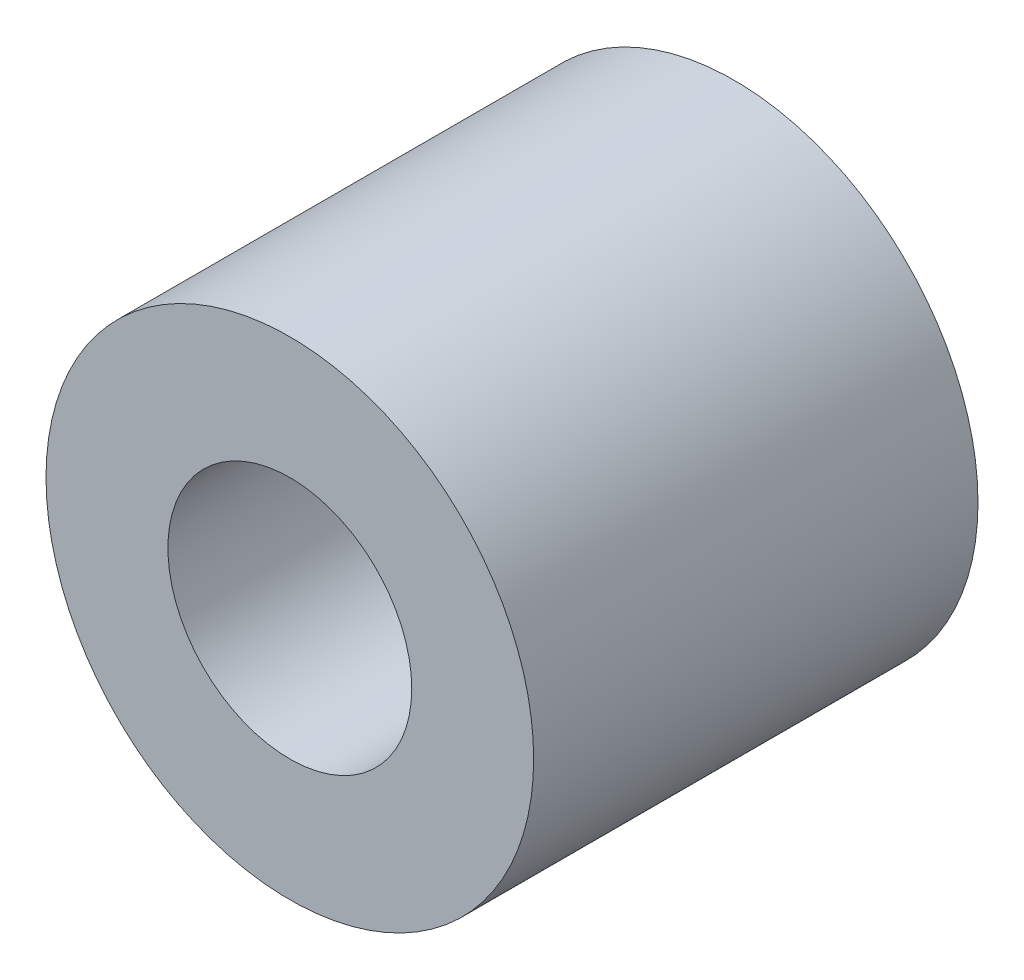
SolidWorks part; units mm, degrees
material "瞎编数据的PLA"
ref_plane "前视基准面" through (0, 0, 0) normal (0, 0, 1) x (1, 0, 0)
ref_plane "上视基准面" through (0, 0, 0) normal (0, 1, 0) x (1, 0, 0)
ref_plane "右视基准面" through (0, 0, 0) normal (1, 0, 0) x (0, 0, -1)
sketch "草图1" plane through (0, 0, 0) normal (0, 0, 1) x (1, 0, 0)
  circle A0 centre (0, 0) radius 2.25
  circle A1 centre (0, 0) radius 4.5
  dimension "D1" = 4.5
  dimension "D2" = 9
extrude "凸台-拉伸1" add sketch "草图1" along normal blind 8.2
